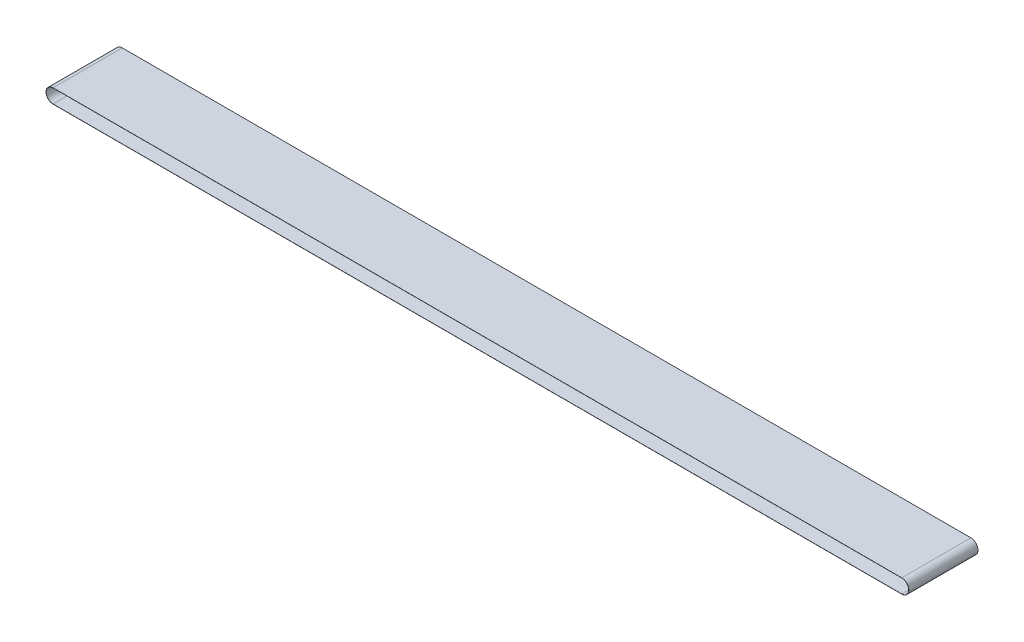
SolidWorks part; units mm, degrees
material "Rubber"
ref_plane "Front Plane" through (0, 0, 0) normal (0, 0, 1) x (1, 0, 0)
ref_plane "Top Plane" through (0, 0, 0) normal (0, 1, 0) x (1, 0, 0)
ref_plane "Right Plane" through (0, 0, 0) normal (1, 0, 0) x (0, 0, -1)
sketch "Sketch1" plane through (0, 0, 0) normal (0, 0, 1) x (1, 0, 0)
  line L0 (0, 0) -> (6134.96, 0) construction
  line L1 (0, 50) -> (6134.96, 50)
  line L2 (0, -50) -> (6134.96, -50)
  line L3 (0, -51.2) -> (6134.96, -51.2)
  line L4 (0, 51.2) -> (6134.96, 51.2)
  arc A0 (0, 50) -> (0, -50) centre (0, 0) ccw
  arc A1 (6134.96, -50) -> (6134.96, 50) centre (6134.96, 0) ccw
  arc A2 (0, 51.2) -> (0, -51.2) centre (0, 0) ccw
  arc A3 (6134.96, -51.2) -> (6134.96, 51.2) centre (6134.96, 0) ccw
  dimension "Overall_Length" = 6134.96
  dimension "D2" = 100
  dimension "D3" = 1.2
extrude "Boss-Extrude1" add sketch "Sketch1" along normal mid plane 500
